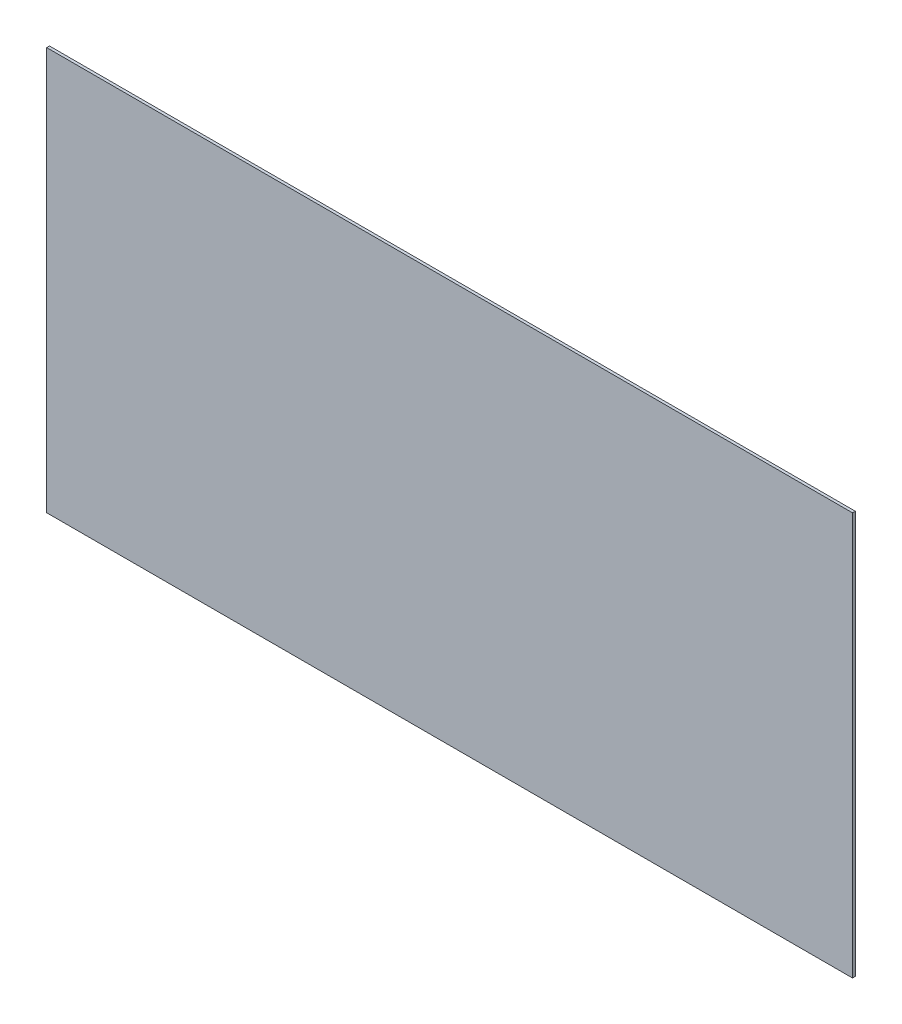
SolidWorks part; units mm, degrees
material "Acrylic (Medium-high impact)"
ref_plane "Front Plane" through (0, 0, 0) normal (0, 0, 1) x (1, 0, 0)
ref_plane "Top Plane" through (0, 0, 0) normal (0, 1, 0) x (1, 0, 0)
ref_plane "Right Plane" through (0, 0, 0) normal (1, 0, 0) x (0, 0, -1)
sketch "Sketch1" plane through (0, 0, 0) normal (0, 0, 1) x (1, 0, 0)
  line L0 (-457.2, 0) -> (457.2, 0)
  line L1 (-457.2, 0) -> (-457.2, 457.2)
  line L2 (-457.2, 457.2) -> (457.2, 457.2)
  line L3 (457.2, 457.2) -> (457.2, 0)
  point P4 (0, 0)
  dimension "D1" = 914.4
  dimension "D2" = 457.2
extrude "Boss-Extrude1" add sketch "Sketch1" against normal blind 3.175
